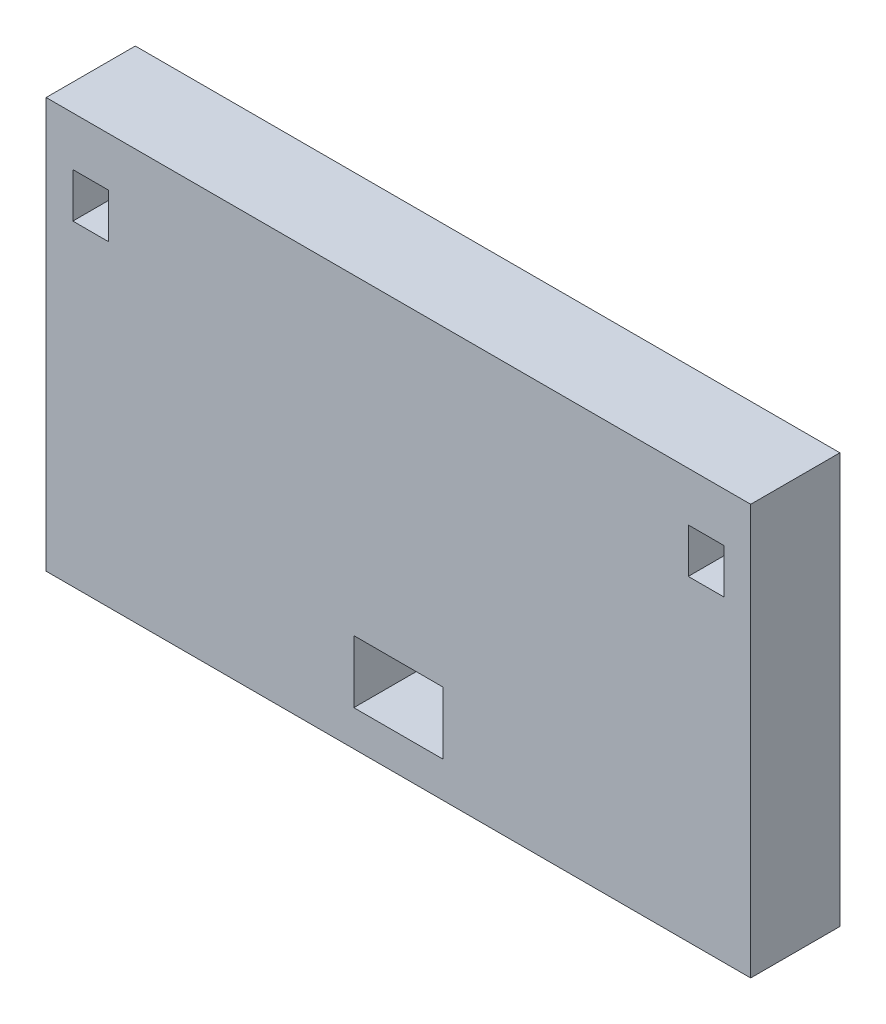
SolidWorks part; units mm, degrees
ref_plane "Front Plane" through (0, 0, 0) normal (0, 0, 1) x (1, 0, 0)
ref_plane "Top Plane" through (0, 0, 0) normal (0, 1, 0) x (1, 0, 0)
ref_plane "Right Plane" through (0, 0, 0) normal (1, 0, 0) x (0, 0, -1)
sketch "Sketch1" plane through (0, 0, 0) normal (0, 0, 1) x (1, 0, 0)
  line L0 (0, -15.5613) -> (0, 51.1465) construction
  line L1 (-39.5, -2.3885) -> (39.5, -2.3885)
  line L2 (-39.5, -2.3885) -> (-39.5, 43.6115)
  line L3 (-39.5, 43.6115) -> (39.5, 43.6115)
  line L4 (39.5, -2.3885) -> (39.5, 43.6115)
  line L5 (-39.5, 20.6115) -> (0, 20.6115) construction
  line L6 (0, 20.6115) -> (39.5, 20.6115) construction
  line L7 (-32.5, 38.1115) -> (-36.5, 38.1115)
  line L8 (5, 1.6115) -> (-5, 1.6115)
  line L9 (5, 1.6115) -> (5, 8.6115)
  line L10 (5, 8.6115) -> (-5, 8.6115)
  line L11 (-5, 1.6115) -> (-5, 8.6115)
  line L12 (5, 1.6115) -> (-5, 8.6115) construction
  line L13 (5, 8.6115) -> (-5, 1.6115) construction
  line L14 (32.5, 33.1074) -> (36.5, 33.1074)
  line L15 (32.5, 33.1074) -> (32.5, 38.1074)
  line L16 (32.5, 38.1074) -> (36.5, 38.1074)
  line L17 (36.5, 33.1074) -> (36.5, 38.1074)
  line L20 (-36.5, 33.1115) -> (-36.5, 38.1115)
  line L21 (-32.5, 33.1074) -> (-36.5, 33.1115)
  line L22 (-32.5, 33.1074) -> (-32.5, 38.1115)
  point P7 (0, 5.1115)
  point P15 (34.5, 20.6115)
  dimension "D1" = 79
  dimension "D2" = 35
  dimension "D3" = 4
  dimension "D4" = 7
  dimension "D5" = 10
  dimension "D6" = 3
  dimension "D7" = 5
  dimension "D8" = 4
extrude "Boss-Extrude1" add sketch "Sketch1" along normal blind 10
